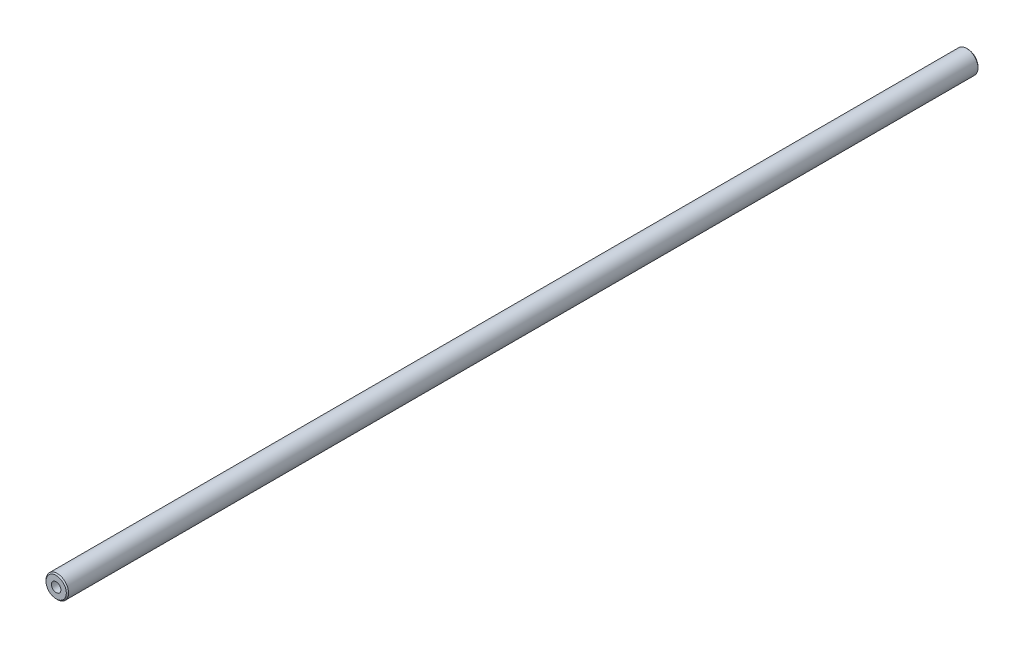
SolidWorks part; units mm, degrees
material "Alloy Steel"
ref_plane "Front Plane" through (0, 0, 0) normal (0, 0, 1) x (1, 0, 0)
ref_plane "Top Plane" through (0, 0, 0) normal (0, 1, 0) x (1, 0, 0)
ref_plane "Right Plane" through (0, 0, 0) normal (1, 0, 0) x (0, 0, -1)
sketch "Sketch1" plane through (0, 0, 0) normal (0, 0, 1) x (1, 0, 0)
  circle A0 centre (0, 0) radius 5
  point P2 (0, 0)
  dimension "D1" = 10
extrude "Boss-Extrude1" add sketch "Sketch1" along normal blind 403.4811
chamfer "Chamfer1" distance 0.5 angle 45 2 edges at (5, 0, 0) (5, 0, 403.4811)
hole_wizard "M5x0.8 Tapped Hole1" positions "3DSketch1" profile "Sketch3" tap size "M5x0.8" standard "ANSI Metric"
sketch3d "3DSketch1"
  line L0 (0, 0, 402.9811) -> (0, 0, 403.4811) construction
  line L1 (0, 0, 0.5) -> (0, 0, 0) construction
  point P0 (0, 0, 403.4811)
  point P4 (0, 0, 0)
sketch "Sketch3" plane through (0, 0, 403.4811) normal (1, 0, 0) x (0, -1, 0)
  line L0 (0, 0) -> (0, 17.6618)
  line L1 (0, 17.6618) -> (2.1, 16.4)
  line L2 (2.1, 16.4) -> (2.1, 0)
  line L5 (2.1, 0) -> (0, 0)
  line L10 (0, 17.6618) -> (-2.1, 16.4) construction
  line L11 (0, -6.35) -> (0, 107.95) construction
  dimension "Tap Drill Dia." = 4.2
  dimension "Tap Drill Depth" = 16.4
  dimension "Drill Angle" = 118
cosmetic thread "Hole Thread1"
cosmetic thread "Hole Thread2"
